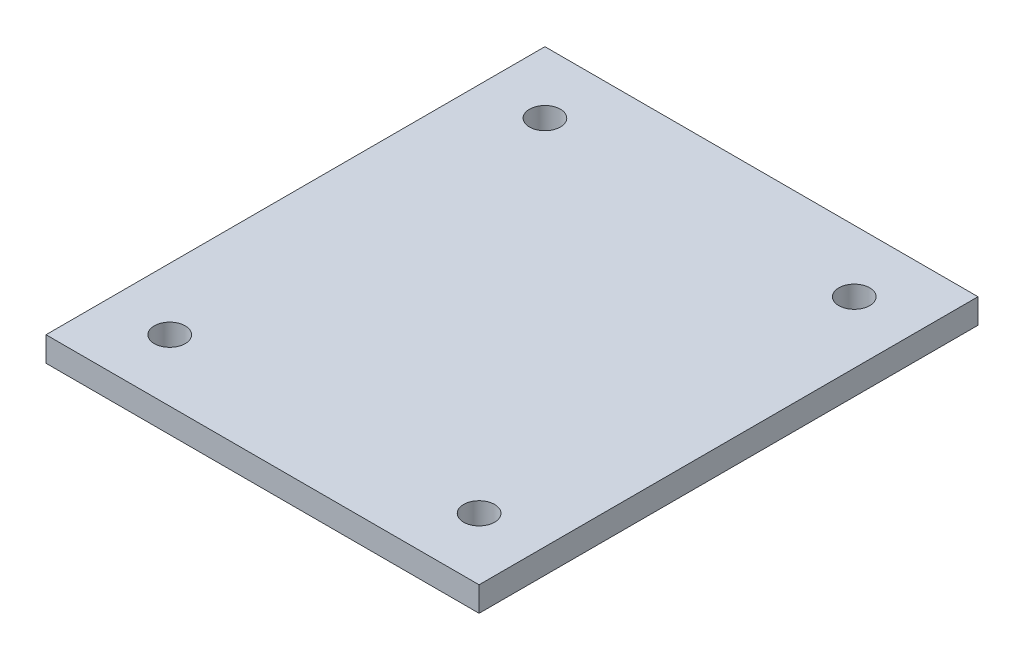
SolidWorks part; units mm, degrees
ref_plane "Front" through (0, 0, 0) normal (0, 0, 1) x (1, 0, 0)
ref_plane "Top" through (0, 0, 0) normal (0, 1, 0) x (1, 0, 0)
ref_plane "Right" through (0, 0, 0) normal (1, 0, 0) x (0, 0, -1)
sketch "Sketch1" plane through (0, 0, 0) normal (0, 1, 0) x (1, 0, 0)
  line L0 (0, 70.64) -> (70, 70.64) construction
  line L1 (0, 0) -> (70, 0)
  line L2 (0, 0) -> (0, 80.64)
  line L3 (0, 80.64) -> (70, 80.64)
  line L4 (70, 0) -> (70, 80.64)
  line L5 (60, 80.64) -> (60, 0) construction
  line L8 (10, 0) -> (10, 80.64) construction
  line L9 (70, 10) -> (0, 10) construction
  dimension "D3" = 10
  dimension "D5" = 10
  dimension "D6" = 10
  dimension "D4" = 50
  dimension "D2" = 60.64
  dimension "D1" = 10
extrude "Boss-Extrude1" add sketch "Sketch1" along normal blind 4
sketch "Sketch2" plane through (0, 4, 0) normal (0, 1, 0) x (1, 0, 0)
  line L9 (0, 70.64) -> (70, 70.64) construction
  line L10 (10, 0) -> (10, 80.64) construction
  line L11 (60, 80.64) -> (60, 0) construction
  line L12 (70, 10) -> (0, 10) construction
  circle A0 centre (10, 70.64) radius 2.5
  circle A1 centre (60, 70.64) radius 2.5
  circle A2 centre (60, 10) radius 2.5
  circle A3 centre (10, 10) radius 2.5
  dimension "D1" = 5
  dimension "D2" = 5
  dimension "D3" = 5
  dimension "D4" = 5
extrude "Cut-Extrude1" cut sketch "Sketch2" against normal through all
sketch "Sketch3" [suppressed] plane through (0, 4, 0) normal (0, 1, 0) x (1, 0, 0)
  line L0 (10, 0) -> (10, 80.64) construction
  line L1 (0, 70.64) -> (70, 70.64) construction
  line L2 (60, 80.64) -> (60, 0) construction
  line L3 (70, 10) -> (0, 10) construction
  circle A0 centre (10, 70.64) radius 3.5
  circle A1 centre (60, 70.64) radius 3.5
  circle A2 centre (60, 10) radius 3.5
  circle A3 centre (10, 10) radius 3.5
  dimension "D1" = 7
  dimension "D2" = 7
  dimension "D3" = 7
  dimension "D4" = 7
extrude "Cut-Extrude2" [suppressed] cut sketch "Sketch3" against normal through all
equation "\"D4@Sketch2\"=\"D1@Sketch2\""
equation "\"D3@Sketch2\"=\"D1@Sketch2\""
equation "\"D2@Sketch2\"=\"D1@Sketch2\""
equation "\"D5@Sketch1\"=\"D3@Sketch1\""
equation "\"D6@Sketch1\"=\"D3@Sketch1\""
equation "\"D4@Sketch3\"=\"D1@Sketch3\""
equation "\"D3@Sketch3\"=\"D1@Sketch3\""
equation "\"D2@Sketch3\"=\"D1@Sketch3\""
equation "\"D1@Sketch1\"=\"D3@Sketch1\""
